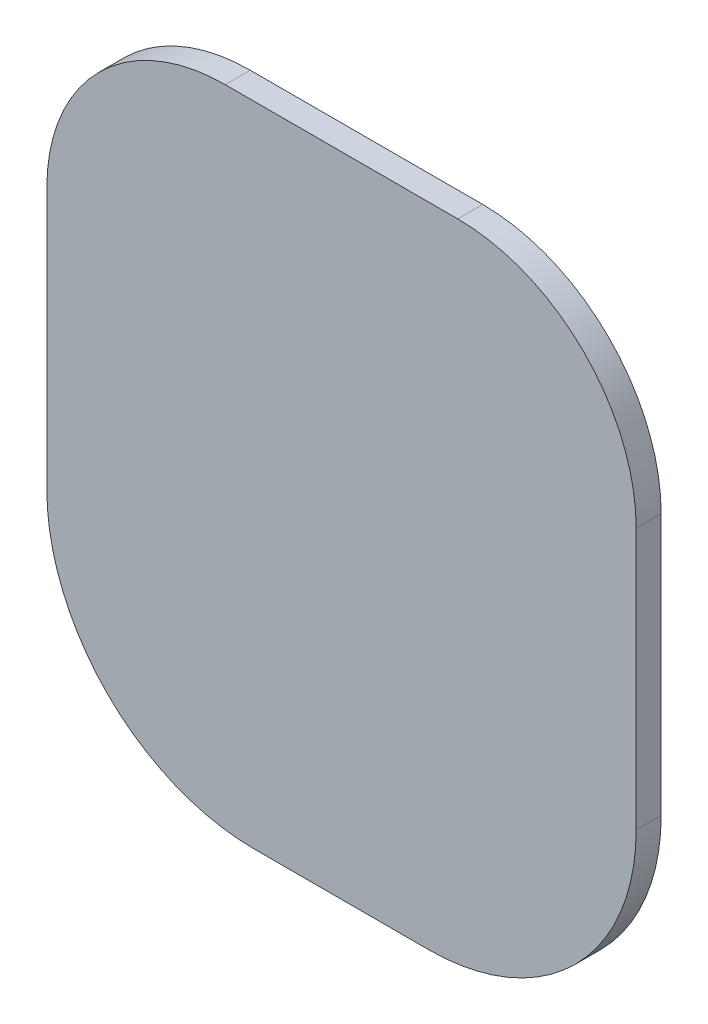
SolidWorks part; units mm, degrees
ref_plane "Front Plane" through (0, 0, 0) normal (0, 0, 1) x (1, 0, 0)
ref_plane "Top Plane" through (0, 0, 0) normal (0, 1, 0) x (1, 0, 0)
ref_plane "Right Plane" through (0, 0, 0) normal (1, 0, 0) x (0, 0, -1)
sketch "Sketch3" plane through (0, 0, 0) normal (0, 0, 1) x (1, 0, 0)
  line L0 (0, 52) -> (0, -68) construction
  line L1 (-55, 52) -> (55, 52) construction
  line L2 (-55, 52) -> (-55, -68) construction
  line L3 (-55, -68) -> (55, -68) construction
  line L4 (55, 52) -> (55, -68) construction
  line L5 (-20, 52) -> (20, 52) construction
  line L6 (-15, -68) -> (15, -68) construction
  line L7 (-55, 17) -> (55, 17) construction
  line L8 (-55, 17) -> (-55, -28) construction
  line L9 (-55, -28) -> (55, -28) construction
  line L10 (55, 17) -> (55, -28) construction
  line L11 (-0.5, -68) -> (0.5, -68) construction
  line L12 (-15, -68) -> (-0.5, -68) construction
  line L13 (0.5, -68) -> (15, -68) construction
  line L14 (-0.5, -68) -> (0.5, -68) construction
  line L15 (-20, 47.7) -> (20, 47.7)
  line L16 (50.7, 17) -> (50.7, -28)
  line L17 (0.5, -63.7) -> (15, -63.7)
  line L18 (-0.5, -63.7) -> (0.5, -63.7)
  line L19 (-15, -63.7) -> (-0.5, -63.7)
  line L20 (-50.7, 17) -> (-50.7, -28)
  arc A0 (-55, 17) -> (-20, 52) centre (-20, 17) cw construction
  arc A1 (20, 52) -> (55, 17) centre (20, 17) cw construction
  arc A2 (-55, -28) -> (-15, -68) centre (-15, -28) ccw construction
  arc A3 (15, -68) -> (55, -28) centre (15, -28) ccw construction
  arc A4 (-50.7, 17) -> (-20, 47.7) centre (-20, 17) cw
  arc A5 (20, 47.7) -> (50.7, 17) centre (20, 17) cw
  arc A6 (15, -63.7) -> (50.7, -28) centre (15, -28) ccw
  arc A7 (-50.7, -28) -> (-15, -63.7) centre (-15, -28) ccw
  point P9 (0, 52)
  point P18 (0, -68)
  point P22 (0, -68)
  dimension "D3" = 40
  dimension "D4" = 35
  dimension "D1" = 120
  dimension "D2" = 110
  dimension "D5" = 1
  dimension "D6" = 52
  dimension "D7" = 4.3
extrude "Boss-Extrude1" add sketch "Sketch3" along normal blind 4.3
